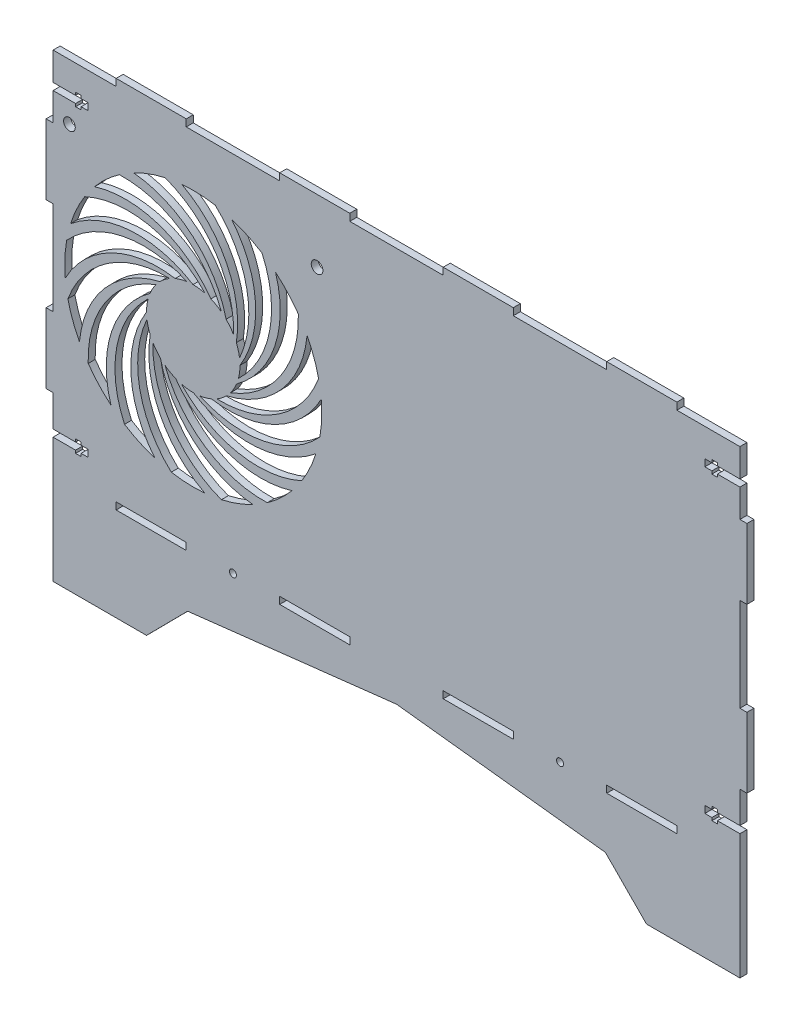
SolidWorks part; units mm, degrees
ref_plane "Front Plane" through (0, 0, 0) normal (0, 0, 1) x (1, 0, 0)
ref_plane "Top Plane" through (0, 0, 0) normal (0, 1, 0) x (1, 0, 0)
ref_plane "Right Plane" through (0, 0, 0) normal (1, 0, 0) x (0, 0, -1)
sketch "Model" plane through (0, 0, 0) normal (0, 0, 1) x (1, 0, 0)
  line L0 (293.8986, 53.2039) -> (284.2686, 53.2039)
  line L1 (284.2686, 53.2039) -> (284.2686, 52.0039)
  line L2 (284.2686, 52.0039) -> (281.8986, 52.0039)
  line L3 (281.8986, 52.0039) -> (281.8986, 53.2039)
  line L4 (281.8986, 53.2039) -> (278.8986, 53.2039)
  line L5 (278.8986, 53.2039) -> (278.8986, 56.2039)
  line L6 (278.8986, 56.2039) -> (281.8986, 56.2039)
  line L7 (281.8986, 56.2039) -> (281.8986, 57.4039)
  line L8 (281.8986, 57.4039) -> (284.2686, 57.4039)
  line L9 (284.2686, 57.4039) -> (284.2686, 56.2039)
  line L10 (284.2686, 56.2039) -> (293.8986, 56.2039)
  line L11 (293.8986, 56.2039) -> (293.8986, 69.7039)
  line L12 (293.8986, 69.7039) -> (296.8986, 69.7039)
  line L13 (296.8986, 69.7039) -> (296.8986, 99.7039)
  line L14 (296.8986, 99.7039) -> (293.8986, 99.7039)
  line L15 (293.8986, 99.7039) -> (293.8986, 139.7039)
  line L16 (293.8986, 139.7039) -> (296.8986, 139.7039)
  line L17 (296.8986, 139.7039) -> (296.8986, 169.7039)
  line L18 (296.8986, 169.7039) -> (293.8986, 169.7039)
  line L19 (293.8986, 169.7039) -> (293.8986, 181.7039)
  line L20 (293.8986, 181.7039) -> (284.2686, 181.7039)
  line L21 (284.2686, 181.7039) -> (284.2686, 180.5039)
  line L22 (284.2686, 180.5039) -> (281.8986, 180.5039)
  line L23 (281.8986, 180.5039) -> (281.8986, 181.7039)
  line L24 (281.8986, 181.7039) -> (278.8986, 181.7039)
  line L25 (278.8986, 181.7039) -> (278.8986, 184.7039)
  line L26 (278.8986, 184.7039) -> (281.8986, 184.7039)
  line L27 (281.8986, 184.7039) -> (281.8986, 185.9039)
  line L28 (281.8986, 185.9039) -> (284.2686, 185.9039)
  line L29 (284.2686, 185.9039) -> (284.2686, 184.7039)
  line L30 (284.2686, 184.7039) -> (293.8986, 184.7039)
  line L31 (293.8986, 184.7039) -> (293.8986, 196.7039)
  line L32 (293.8986, 196.7039) -> (266.8986, 196.7039)
  line L33 (266.8986, 196.7039) -> (266.8986, 199.7039)
  line L34 (266.8986, 199.7039) -> (236.8986, 199.7039)
  line L35 (236.8986, 199.7039) -> (236.8986, 196.7039)
  line L36 (236.8986, 196.7039) -> (196.8986, 196.7039)
  line L37 (196.8986, 196.7039) -> (196.8986, 199.7039)
  line L38 (196.8986, 199.7039) -> (166.8986, 199.7039)
  line L39 (166.8986, 199.7039) -> (166.8986, 196.7039)
  line L40 (166.8986, 196.7039) -> (126.8986, 196.7039)
  line L41 (126.8986, 196.7039) -> (126.8986, 199.7039)
  line L42 (126.8986, 199.7039) -> (96.8986, 199.7039)
  line L43 (96.8986, 199.7039) -> (96.8986, 196.7039)
  line L44 (96.8986, 196.7039) -> (56.8986, 196.7039)
  line L45 (56.8986, 196.7039) -> (56.8986, 199.7039)
  line L46 (56.8986, 199.7039) -> (26.8986, 199.7039)
  line L47 (26.8986, 199.7039) -> (26.8986, 196.7039)
  line L48 (26.8986, 196.7039) -> (-0.1014, 196.7039)
  line L49 (-0.1014, 196.7039) -> (-0.1014, 184.7039)
  line L50 (-0.1014, 169.7039) -> (-3.1014, 169.7039)
  line L51 (-3.1014, 169.7039) -> (-3.1014, 139.7039)
  line L52 (-3.1014, 139.7039) -> (-0.1014, 139.7039)
  line L53 (-0.1014, 139.7039) -> (-0.1014, 99.7039)
  line L54 (-0.1014, 99.7039) -> (-3.1014, 99.7039)
  line L55 (-3.1014, 99.7039) -> (-3.1014, 69.7039)
  line L56 (-3.1014, 69.7039) -> (-0.1014, 69.7039)
  line L57 (-0.1014, 69.7039) -> (-0.1014, 56.2039)
  line L58 (253.8986, -0.2961) -> (293.8986, -0.2961)
  line L59 (293.8986, -0.2961) -> (293.8986, 53.2039)
  line L60 (196.8986, 39.7039) -> (196.8986, 42.7039)
  line L61 (196.8986, 42.7039) -> (166.8986, 42.7039)
  line L62 (166.8986, 42.7039) -> (166.8986, 39.7039)
  line L63 (166.8986, 39.7039) -> (196.8986, 39.7039)
  line L64 (126.8986, 39.7039) -> (126.8986, 42.7039)
  line L65 (126.8986, 42.7039) -> (96.8986, 42.7039)
  line L66 (96.8986, 42.7039) -> (96.8986, 39.7039)
  line L67 (96.8986, 39.7039) -> (126.8986, 39.7039)
  line L68 (266.8986, 39.7039) -> (266.8986, 42.7039)
  line L69 (266.8986, 42.7039) -> (236.8986, 42.7039)
  line L70 (236.8986, 42.7039) -> (236.8986, 39.7039)
  line L71 (236.8986, 39.7039) -> (266.8986, 39.7039)
  line L72 (56.8986, 39.7039) -> (56.8986, 42.7039)
  line L73 (56.8986, 42.7039) -> (26.8986, 42.7039)
  line L74 (26.8986, 42.7039) -> (26.8986, 39.7039)
  line L75 (26.8986, 39.7039) -> (56.8986, 39.7039)
  line L76 (39.8986, -0.2961) -> (57.4817, 17.4756)
  line L77 (57.4817, 17.4756) -> (146.8986, 27.7039)
  line L78 (146.8986, 27.7039) -> (236.3155, 17.4756)
  line L79 (236.3155, 17.4756) -> (253.8986, -0.2961)
  line L80 (-0.1014, -0.2961) -> (39.8986, -0.2961)
  line L81 (-0.1014, 184.7039) -> (9.5286, 184.7039)
  line L82 (9.5286, 184.7039) -> (9.5286, 185.9039)
  line L83 (9.5286, 185.9039) -> (11.8986, 185.9039)
  line L84 (11.8986, 185.9039) -> (11.8986, 184.7039)
  line L85 (11.8986, 184.7039) -> (14.8986, 184.7039)
  line L86 (14.8986, 184.7039) -> (14.8986, 181.7039)
  line L87 (14.8986, 181.7039) -> (11.8986, 181.7039)
  line L88 (11.8986, 181.7039) -> (11.8986, 180.5039)
  line L89 (11.8986, 180.5039) -> (9.5286, 180.5039)
  line L90 (9.5286, 180.5039) -> (9.5286, 181.7039)
  line L91 (9.5286, 181.7039) -> (-0.1014, 181.7039)
  line L92 (-0.1014, 181.7039) -> (-0.1014, 169.7039)
  line L93 (-0.1014, 56.2039) -> (9.5286, 56.2039)
  line L94 (9.5286, 56.2039) -> (9.5286, 57.4039)
  line L95 (9.5286, 57.4039) -> (11.8986, 57.4039)
  line L96 (11.8986, 57.4039) -> (11.8986, 56.2039)
  line L97 (11.8986, 56.2039) -> (14.8986, 56.2039)
  line L98 (14.8986, 56.2039) -> (14.8986, 53.2039)
  line L99 (14.8986, 53.2039) -> (11.8986, 53.2039)
  line L100 (11.8986, 53.2039) -> (11.8986, 52.0039)
  line L101 (11.8986, 52.0039) -> (9.5286, 52.0039)
  line L102 (9.5286, 52.0039) -> (9.5286, 53.2039)
  line L103 (9.5286, 53.2039) -> (-0.1014, 53.2039)
  line L104 (-0.1014, 53.2039) -> (-0.1014, -0.2961)
  circle A0 centre (76.8986, 41.2039) radius 1.5
  circle A1 centre (216.8986, 41.2039) radius 1.5
  circle A2 centre (6.8986, 172.7039) radius 2.5
  circle A4 centre (112.8986, 172.7039) radius 2.5
  arc A6 (6.2342, 107.6567) -> (11.1809, 94.1778) centre (59.8986, 119.7039) ccw
  arc A7 (49.7987, 136.9663) -> (6.2342, 107.6567) centre (48.4181, 91.9875) ccw
  arc A8 (49.7987, 136.9663) -> (45.675, 133.7641) centre (59.8986, 119.7039) ccw
  arc A9 (45.675, 133.7641) -> (11.1809, 94.1778) centre (55.9828, 89.9605) ccw
  arc A10 (71.9458, 66.0395) -> (85.4247, 70.9861) centre (59.8986, 119.7039) ccw
  arc A11 (42.6362, 109.604) -> (71.9458, 66.0395) centre (87.615, 108.2234) ccw
  arc A12 (42.6362, 109.604) -> (45.8384, 105.4803) centre (59.8986, 119.7039) ccw
  arc A13 (45.8384, 105.4803) -> (85.4247, 70.9861) centre (89.642, 115.7881) ccw
  arc A14 (113.563, 131.7511) -> (108.6164, 145.23) centre (59.8986, 119.7039) ccw
  arc A15 (69.9985, 102.4415) -> (113.563, 131.7511) centre (71.3791, 147.4203) ccw
  arc A16 (69.9985, 102.4415) -> (74.1222, 105.6437) centre (59.8986, 119.7039) ccw
  arc A17 (74.1222, 105.6437) -> (108.6164, 145.23) centre (63.8144, 149.4472) ccw
  arc A18 (47.8514, 173.3683) -> (34.3725, 168.4216) centre (59.8986, 119.7039) ccw
  arc A19 (77.161, 129.8038) -> (47.8514, 173.3683) centre (32.1822, 131.1844) ccw
  arc A20 (77.161, 129.8038) -> (73.9588, 133.9275) centre (59.8986, 119.7039) ccw
  arc A21 (73.9588, 133.9275) -> (34.3725, 168.4216) centre (30.1553, 123.6197) ccw
  arc A22 (79.7121, 122.429) -> (69.3049, 173.8936) centre (38.6854, 140.9171) ccw
  arc A23 (79.7121, 122.429) -> (78.3317, 127.4642) centre (59.8986, 119.7039) ccw
  arc A24 (78.3317, 127.4642) -> (54.9591, 174.4816) centre (33.9179, 134.7039) ccw
  arc A25 (69.3049, 173.8936) -> (54.9591, 174.4816) centre (59.8986, 119.7039) ccw
  arc A26 (114.0883, 110.2976) -> (114.6764, 124.6434) centre (59.8986, 119.7039) ccw
  arc A27 (62.6237, 99.8904) -> (114.0883, 110.2976) centre (81.1118, 140.9171) ccw
  arc A28 (62.6237, 99.8904) -> (67.6589, 101.2708) centre (59.8986, 119.7039) ccw
  arc A29 (67.6589, 101.2708) -> (114.6764, 124.6434) centre (74.8986, 145.6846) ccw
  arc A30 (50.4923, 65.5142) -> (64.8382, 64.9262) centre (59.8986, 119.7039) ccw
  arc A31 (40.0851, 116.9788) -> (50.4923, 65.5142) centre (81.1118, 98.4907) ccw
  arc A32 (40.0851, 116.9788) -> (41.4656, 111.9436) centre (59.8986, 119.7039) ccw
  arc A33 (41.4656, 111.9436) -> (64.8382, 64.9262) centre (85.8794, 104.7039) ccw
  arc A34 (5.7089, 129.1102) -> (5.1209, 114.7643) centre (59.8986, 119.7039) ccw
  arc A35 (57.1736, 139.5174) -> (5.7089, 129.1102) centre (38.6854, 98.4907) ccw
  arc A36 (57.1736, 139.5174) -> (52.1383, 138.1369) centre (59.8986, 119.7039) ccw
  arc A37 (52.1383, 138.1369) -> (5.1209, 114.7643) centre (44.8986, 93.7231) ccw
  arc A38 (14.9295, 88.0372) -> (24.6577, 77.4774) centre (59.8986, 119.7039) ccw
  arc A39 (43.9615, 131.7872) -> (14.9295, 88.0372) centre (59.8986, 89.7039) ccw
  arc A40 (43.9615, 131.7872) -> (41.3771, 127.2507) centre (59.8986, 119.7039) ccw
  arc A41 (41.3771, 127.2507) -> (24.6577, 77.4774) centre (67.6632, 90.7261) ccw
  arc A42 (91.5653, 74.7348) -> (102.1251, 84.463) centre (59.8986, 119.7039) ccw
  arc A43 (47.8153, 103.7667) -> (91.5653, 74.7348) centre (89.8986, 119.7039) ccw
  arc A44 (47.8153, 103.7667) -> (52.3518, 101.1824) centre (59.8986, 119.7039) ccw
  arc A45 (52.3518, 101.1824) -> (102.1251, 84.463) centre (88.8764, 127.4685) ccw
  arc A46 (104.8677, 151.3705) -> (95.1395, 161.9304) centre (59.8986, 119.7039) ccw
  arc A47 (75.8358, 107.6206) -> (104.8677, 151.3705) centre (59.8986, 149.7039) ccw
  arc A48 (75.8358, 107.6206) -> (78.4201, 112.1571) centre (59.8986, 119.7039) ccw
  arc A49 (78.4201, 112.1571) -> (95.1395, 161.9304) centre (52.1341, 148.6817) ccw
  arc A50 (28.232, 164.673) -> (17.6721, 154.9448) centre (59.8986, 119.7039) ccw
  arc A51 (71.982, 135.641) -> (28.232, 164.673) centre (29.8986, 119.7039) ccw
  arc A52 (71.982, 135.641) -> (67.4454, 138.2254) centre (59.8986, 119.7039) ccw
  arc A53 (67.4454, 138.2254) -> (17.6721, 154.9448) centre (30.9208, 111.9393) ccw
  arc A54 (79.2467, 114.6392) -> (89.3264, 166.169) centre (48.4181, 147.4203) ccw
  arc A55 (79.2467, 114.6392) -> (79.8983, 119.8195) centre (59.8986, 119.7039) ccw
  arc A56 (79.8983, 119.8195) -> (76.2976, 172.2022) centre (41.6358, 143.5045) ccw
  arc A57 (89.3264, 166.169) -> (76.2976, 172.2022) centre (59.8986, 119.7039) ccw
  arc A58 (106.3637, 90.2761) -> (112.3969, 103.3049) centre (59.8986, 119.7039) ccw
  arc A59 (54.834, 100.3558) -> (106.3637, 90.2761) centre (87.615, 131.1844) ccw
  arc A60 (54.834, 100.3558) -> (60.0142, 99.7042) centre (59.8986, 119.7039) ccw
  arc A61 (60.0142, 99.7042) -> (112.3969, 103.3049) centre (83.6992, 137.9667) ccw
  arc A62 (30.4709, 73.2388) -> (43.4996, 67.2056) centre (59.8986, 119.7039) ccw
  arc A63 (40.5505, 124.7686) -> (30.4709, 73.2388) centre (71.3791, 91.9875) ccw
  arc A64 (40.5505, 124.7686) -> (39.8989, 119.5883) centre (59.8986, 119.7039) ccw
  arc A65 (39.8989, 119.5883) -> (43.4996, 67.2056) centre (78.1614, 95.9033) ccw
  arc A66 (13.4335, 149.1317) -> (7.4003, 136.1029) centre (59.8986, 119.7039) ccw
  arc A67 (64.9633, 139.052) -> (13.4335, 149.1317) centre (32.1822, 108.2234) ccw
  arc A68 (64.9633, 139.052) -> (59.783, 139.7036) centre (59.8986, 119.7039) ccw
  arc A69 (59.783, 139.7036) -> (7.4003, 136.1029) centre (36.098, 101.4411) ccw
extrude "Boss-Extrude1" add sketch "Model" along normal blind 3
